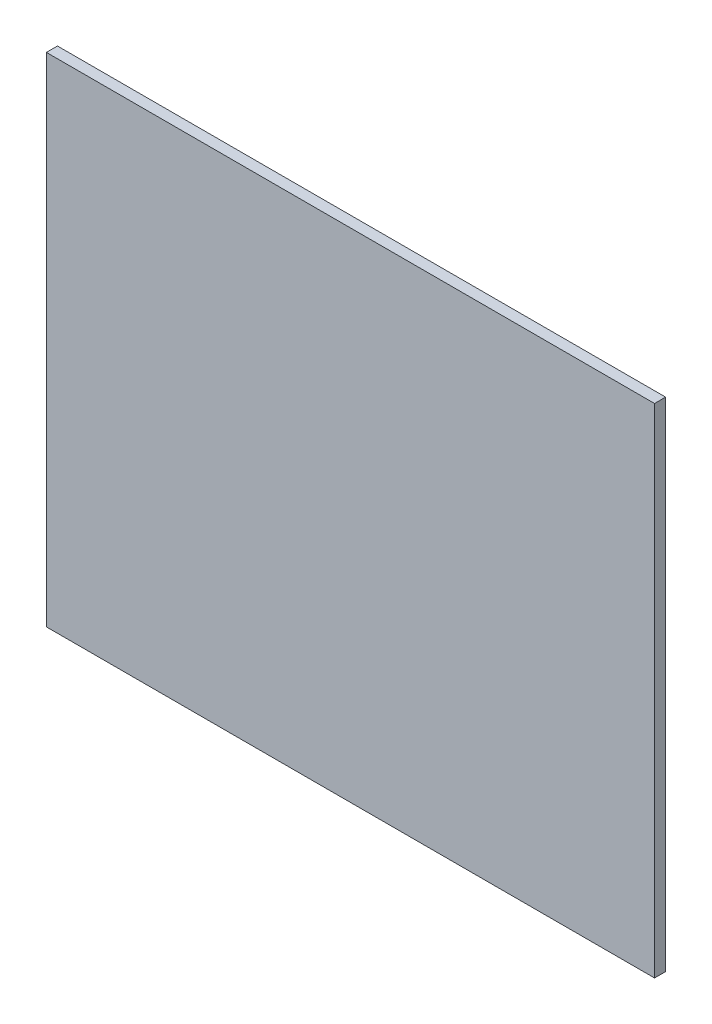
SolidWorks part; units mm, degrees
ref_plane "Front Plane" through (0, 0, 0) normal (0, 0, 1) x (1, 0, 0)
ref_plane "Top Plane" through (0, 0, 0) normal (0, 1, 0) x (1, 0, 0)
ref_plane "Right Plane" through (0, 0, 0) normal (1, 0, 0) x (0, 0, -1)
sketch "Sketch1" plane through (0, 0, 0) normal (0, 0, 1) x (1, 0, 0)
  line L1 (-27.5, -22.5) -> (27.5, -22.5)
  line L2 (-27.5, -22.5) -> (-27.5, 22.5)
  line L3 (-27.5, 22.5) -> (27.5, 22.5)
  line L4 (27.5, -22.5) -> (27.5, 22.5)
  line L5 (-27.5, -22.5) -> (27.5, 22.5) construction
  line L6 (-27.5, 22.5) -> (27.5, -22.5) construction
  point P0 (0, 0)
  dimension "D1" = 55
  dimension "D2" = 45
extrude "Boss-Extrude1" add sketch "Sketch1" along normal blind 1
